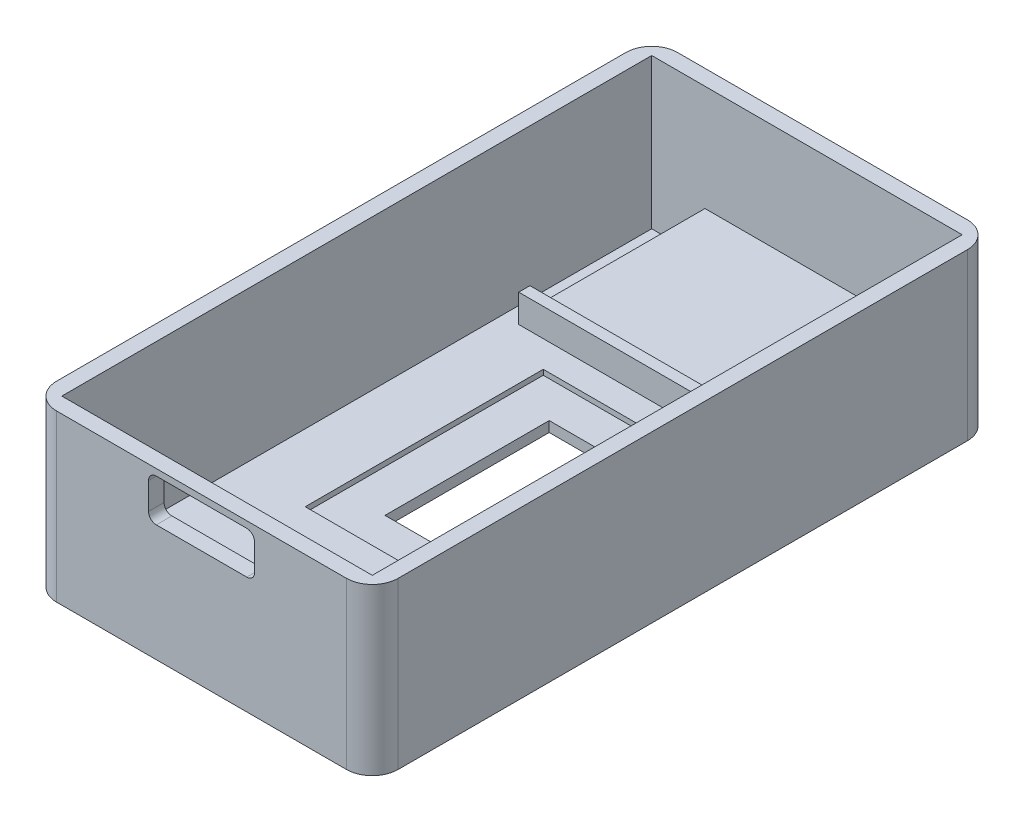
SolidWorks part; units mm, degrees
ref_plane "Front Plane" through (0, 0, 0) normal (0, 0, 1) x (1, 0, 0)
ref_plane "Top Plane" through (0, 0, 0) normal (0, 1, 0) x (1, 0, 0)
ref_plane "Right Plane" through (0, 0, 0) normal (1, 0, 0) x (0, 0, -1)
sketch "Sketch1" plane through (0, 0, 0) normal (0, 1, 0) x (1, 0, 0)
  line L1 (0.4896, 11.2612) -> (33.4896, 11.2612)
  line L2 (0.4896, 11.2612) -> (0.4896, -48.7388)
  line L3 (0.4896, -48.7388) -> (33.4896, -48.7388)
  line L4 (33.4896, 11.2612) -> (33.4896, -48.7388)
  dimension "D1" = 60
  dimension "D2" = 33
extrude "Boss-Extrude1" add sketch "Sketch1" along normal blind 16
shell "Shell1" thickness 1.5
sketch "Sketch3" [suppressed] plane through (0, 0, 48.7388) normal (0, 0, 1) x (1, 0, 0)
  line L0 (21.6896, 11.64) -> (21.6896, 10.04) construction
  line L1 (11.6896, 15.2324) -> (21.6896, 15.2324)
  line L2 (11.6896, 15.2324) -> (11.6896, 10.84)
  line L3 (11.6896, 10.84) -> (21.6896, 10.84)
  line L4 (21.6896, 15.2324) -> (21.6896, 10.84)
  line L5 (11.6896, 13.0362) -> (-49988.3104, 13.0362) construction
  line L7 (16.9896, 16) -> (16.9896, -49984) construction
  line L8 (0.4896, 16) -> (33.4896, 16) construction
  point P8 (11.6896, 13.0362)
  point P13 (16.9896, 16)
extrude "Cut-Extrude1" [suppressed] cut sketch "Sketch3" against normal blind 10
sketch "Sketch4" plane through (0, 0, 48.7388) normal (0, 0, 1) x (1, 0, 0)
  line L0 (16.9896, 16) -> (16.9896, -49984) construction
  line L1 (0.4896, 16) -> (33.4896, 16) construction
  line L2 (0.4896, 0) -> (33.4896, 0) construction
  line L3 (16.9896, 13.3274) -> (50016.9896, 13.3274) construction
  line L6 (12.6191, 11.2875) -> (21.3601, 11.2875)
  line L7 (11.8691, 12.0375) -> (11.8691, 14.6173)
  line L8 (12.6191, 15.3673) -> (21.3601, 15.3673)
  line L9 (22.1101, 12.0375) -> (22.1101, 14.6173)
  line L10 (11.8691, 11.2875) -> (22.1101, 15.3673) construction
  line L11 (11.8691, 15.3673) -> (22.1101, 11.2875) construction
  arc A0 (21.3601, 15.3673) -> (22.1101, 14.6173) centre (21.3601, 14.6173) cw
  arc A1 (21.3601, 11.2875) -> (22.1101, 12.0375) centre (21.3601, 12.0375) ccw
  arc A2 (12.6191, 11.2875) -> (11.8691, 12.0375) centre (12.6191, 12.0375) cw
  arc A3 (11.8691, 14.6173) -> (12.6191, 15.3673) centre (12.6191, 14.6173) cw
  point P4 (16.9896, 16)
  point P7 (16.9896, 0)
  point P10 (16.9896, 13.3274)
  dimension "D1" = 0.75
extrude "Cut-Extrude2" cut sketch "Sketch4" against normal blind 10
sketch "Sketch5" plane through (0, 0, 0) normal (0, -1, 0) x (1, 0, 0)
  line L0 (30.1396, -5.6112) -> (-49969.8604, -5.6112) construction
  line L1 (28.8896, -6.8612) -> (28.8896, 49993.1388) construction
  line L2 (5.0896, -6.8612) -> (5.0896, 49993.1388) construction
  line L3 (30.1396, 45.1888) -> (-49969.8604, 45.1888) construction
  circle A1 centre (28.8896, 45.1888) radius 1.25
  circle A2 centre (5.0896, 45.1888) radius 1.25
  circle A3 centre (28.8896, -5.6112) radius 1.25
  circle A4 centre (5.0896, -5.6112) radius 1.25
extrude "Cut-Extrude3" cut sketch "Sketch5" against normal blind 3 and the other way through all
sketch "Sketch6" plane through (0, 0, -9.7612) normal (0, 0, 1) x (1, 0, 0)
  line L1 (7.1377, 5.7675) -> (26.6989, 5.7675)
  line L2 (7.1377, 5.7675) -> (7.1377, 5.0632)
  line L3 (7.1377, 5.0632) -> (26.6989, 5.0632)
  line L4 (26.6989, 5.7675) -> (26.6989, 5.0632)
extrude "Boss-Extrude2" add sketch "Sketch6" along normal blind 18
sketch "Sketch7" plane through (0, 5.7675, 0) normal (0, 1, 0) x (1, 0, 0)
  line L0 (7.1377, -8.2388) -> (7.1377, 9.7612) construction
  line L1 (26.6989, -8.2388) -> (7.1377, -8.2388)
  line L2 (26.6989, -8.2388) -> (26.6989, -7.1527)
  line L3 (26.6989, -7.1527) -> (7.1377, -7.1527)
  line L4 (7.1377, -8.2388) -> (7.1377, -7.1527)
extrude "Boss-Extrude3" add sketch "Sketch7" along normal blind 2
sketch "Sketch9" plane through (0, 1.5, 0) normal (0, 1, 0) x (1, 0, 0)
  line L0 (1.9896, -18.7388) -> (50001.9896, -18.7388) construction
  line L1 (1.9896, 9.7612) -> (1.9896, -47.2388) construction
  line L2 (31.9896, -47.2388) -> (31.9896, 9.7612) construction
  line L3 (16.9896, 9.7612) -> (16.9896, -49990.2388) construction
  line L4 (31.9896, 9.7612) -> (1.9896, 9.7612) construction
  line L5 (1.9896, -47.2388) -> (31.9896, -47.2388) construction
  line L7 (8.5096, -30.2388) -> (25.4696, -30.2388)
  line L8 (8.5096, -30.2388) -> (8.5096, -7.2388)
  line L9 (8.5096, -7.2388) -> (25.4696, -7.2388)
  line L10 (25.4696, -30.2388) -> (25.4696, -7.2388)
  line L11 (8.5096, -30.2388) -> (25.4696, -7.2388) construction
  line L12 (8.5096, -7.2388) -> (25.4696, -30.2388) construction
  point P4 (1.9896, -18.7388)
  point P7 (31.9896, -18.7388)
  point P12 (16.9896, 9.7612)
  point P15 (16.9896, -47.2388)
  point P16 (16.9896, -18.7388)
  dimension "D1" = 23
extrude "Cut-Extrude4" cut sketch "Sketch9" against normal blind 0.5
sketch "Sketch11" plane through (0, 0, 0) normal (0, -1, 0) x (1, 0, 0)
  line L0 (21.4896, 27.0888) -> (21.5896, 23.9508) construction
  line L1 (12.5879, 10.742) -> (21.5048, 10.742)
  line L2 (12.5879, 10.742) -> (12.5879, 26.6109)
  line L3 (12.5879, 26.6109) -> (21.5048, 26.6109)
  line L4 (21.5048, 10.742) -> (21.5048, 26.6109)
extrude "Cut-Extrude6" cut sketch "Sketch11" against normal up to next
fillet "Fillet1" radius 2.5 4 edges at (33.4896, 8, 48.7388) (0.4896, 8, 48.7388) (33.4896, 8, -11.2612) (0.4896, 8, -11.2612)
